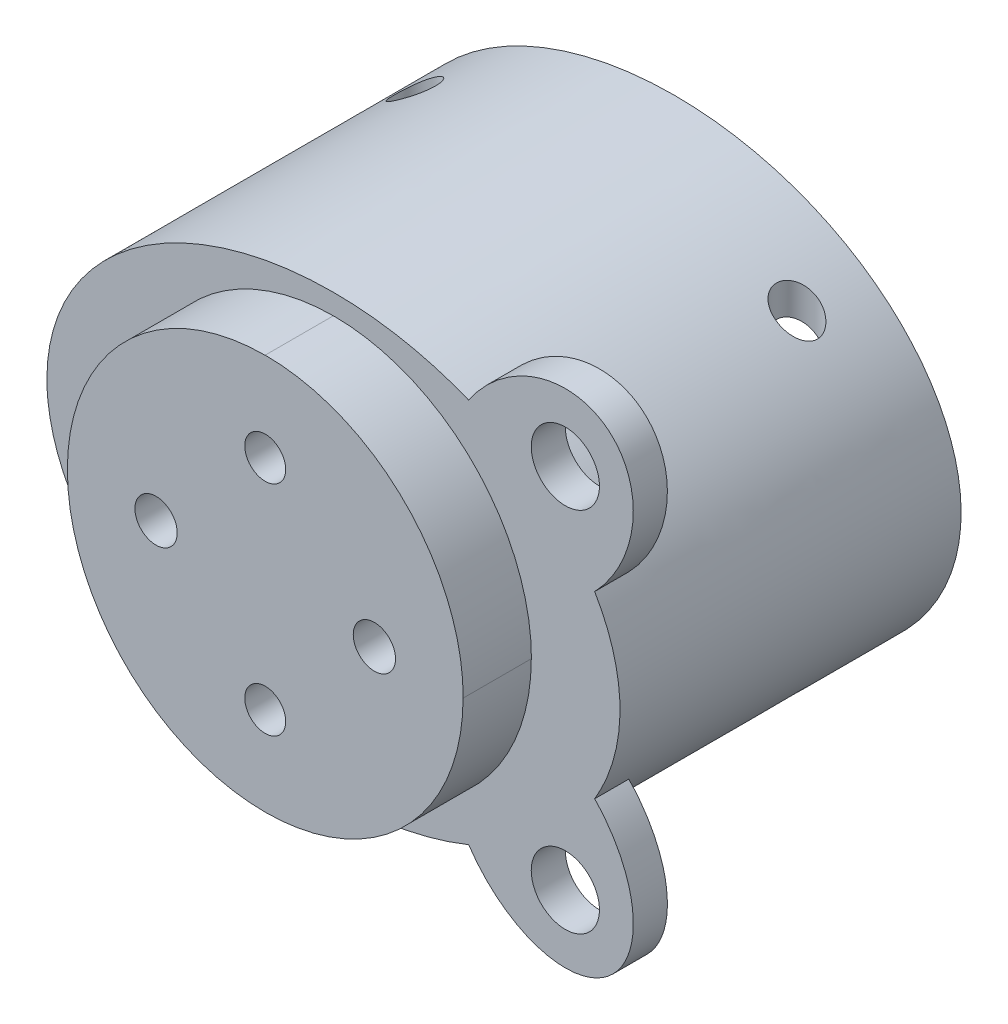
SolidWorks part; units mm, degrees
ref_plane "前视基准面" through (0, 0, 0) normal (0, 0, 1) x (1, 0, 0)
ref_plane "上视基准面" through (0, 0, 0) normal (0, 1, 0) x (1, 0, 0)
ref_plane "右视基准面" through (0, 0, 0) normal (1, 0, 0) x (0, 0, -1)
sketch "草图1" plane through (0, 0, 0) normal (0, 0, 1) x (1, 0, 0)
  circle A0 centre (0, 0) radius 14.5
extrude "凸台-拉伸1" add sketch "草图1" along normal blind 5
sketch "草图2" plane through (0, 0, 0) normal (0, 0, -1) x (-1, 0, 0)
  line L0 (-14.51, 0) -> (0, 0)
  line L1 (0, 0) -> (0, 14.51)
  arc A0 (-14.51, 0) -> (0, 14.51) centre (0, 0) cw
extrude "凸台-拉伸2" add sketch "草图2" against normal blind 5
sketch "草图10" plane through (0, 0, 0) normal (0, 0, -1) x (-1, 0, 0)
  ellipse E0 centre (0, 0) end of major axis (-19, 0) minor radius 14
  ellipse E1 centre (0, 0) end of major axis (21, 0) minor radius 16
extrude "凸台-拉伸4" add sketch "草图10" along normal blind 25
sketch "草图12" plane through (0, 0, 0) normal (0, 0, -1) x (-1, 0, 0)
  ellipse E0 centre (0, 0) end of major axis (19, 0) minor radius 14
  ellipse E1 centre (0, 0) end of major axis (-19, 0) minor radius 14 (-5.5837, -13.3818) -> (5.5837, -13.3818) ccw construction
extrude "凸台-拉伸5" add sketch "草图12" along normal blind 2
sketch "草图15" plane through (0, 0, 0) normal (0, 0, 1) x (1, 0, 0)
  line L0 (9.8683, 14.0419) -> (19.1013, 6.5346)
  line L1 (20.0985, 17.3658) -> (15.1323, 11.0939) construction
  line L2 (21, 0) -> (-21, 0) construction
  line L3 (9.8683, -14.0419) -> (19.1013, -6.5346)
  circle A0 centre (16.9946, 13.4458) radius 2.5
  circle A1 centre (16.9946, -13.4458) radius 2.5
  ellipse E0 centre (15.1323, 11.0939) end of major axis (10.1661, 4.822) minor radius 6 (19.1013, 6.5346) -> (9.8683, 14.0419) ccw
  ellipse E1 centre (0, 0) end of major axis (-21, 0) minor radius 16 construction
  ellipse E2 centre (15.1323, -11.0939) end of major axis (20.0985, -17.3658) minor radius 6 (19.1013, -6.5346) -> (9.8683, -14.0419) cw
  dimension "D1" = 5
extrude "凸台-拉伸7" add sketch "草图15" against normal blind 2.5
sketch "草图16" plane through (0, 0, 0) normal (0, -1, 0) x (1, 0, 0)
  line L0 (0, 5) -> (0, -25.7566) construction
  line L1 (-0.5568, -19.9682) -> (-22.0981, -19.9682) construction
  circle A0 centre (14, -19.9682) radius 1.5
  circle A1 centre (-14, -19.9682) radius 1.5
  dimension "D1" = 14
extrude "切除-拉伸6" cut sketch "草图16" against normal up to next and the other way up to next
sketch "草图17" plane through (0, 0, 5) normal (0, 0, 1) x (1, 0, 0)
  line L0 (-14.5, 0) -> (14.5, 0) construction
  line L1 (0, 14.5) -> (0, -14.5) construction
  circle A0 centre (0, 0) radius 14.5 construction
  circle A1 centre (-8, 0) radius 1.55
  circle A2 centre (8, 0) radius 1.55
  circle A3 centre (0, 8) radius 1.5
  circle A4 centre (0, -8) radius 1.5
  dimension "D1" = 8
  dimension "D2" = 8
extrude "切除-拉伸7" cut sketch "草图17" against normal up to next
sketch "草图19" plane through (0, 0, -2) normal (0, 0, -1) x (-1, 0, 0)
  line L1 (-5.4231, -1.5449) -> (-5.3736, 1.4592)
  line L2 (-5.3736, 1.4592) -> (-7.9505, 3.0041)
  line L3 (-7.9505, 3.0041) -> (-10.5769, 1.5449)
  line L4 (-10.5769, 1.5449) -> (-10.6264, -1.4592)
  line L5 (-10.6264, -1.4592) -> (-8.0495, -3.0041)
  line L6 (-8.0495, -3.0041) -> (-5.4231, -1.5449)
  line L7 (5.4584, -1.7177) -> (8.2168, -3.06)
  line L8 (8.2168, -3.06) -> (10.7584, -1.3422)
  line L9 (10.7584, -1.3422) -> (10.5416, 1.7177)
  line L10 (10.5416, 1.7177) -> (7.7832, 3.06)
  line L11 (7.7832, 3.06) -> (5.2416, 1.3422)
  line L12 (5.2416, 1.3422) -> (5.4584, -1.7177)
  line L13 (0, 4.88) -> (2.702, 6.44)
  line L14 (2.702, 6.44) -> (2.702, 9.56)
  line L15 (2.702, 9.56) -> (0, 11.12)
  line L16 (0, 11.12) -> (-2.702, 9.56)
  line L17 (-2.702, 9.56) -> (-2.702, 6.44)
  line L18 (-2.702, 6.44) -> (0, 4.88)
  line L19 (0, -11.12) -> (2.702, -9.56)
  line L20 (2.702, -9.56) -> (2.702, -6.44)
  line L21 (2.702, -6.44) -> (0, -4.88)
  line L22 (0, -4.88) -> (-2.702, -6.44)
  line L23 (-2.702, -6.44) -> (-2.702, -9.56)
  line L24 (-2.702, -9.56) -> (0, -11.12)
  circle A0 centre (-8, 0) radius 2.602 construction
  circle A1 centre (8, 0) radius 2.6566 construction
  circle A2 centre (0, 8) radius 2.702 construction
  circle A3 centre (0, -8) radius 2.702 construction
extrude "切除-拉伸10" cut sketch "草图19" against normal blind 2.5
